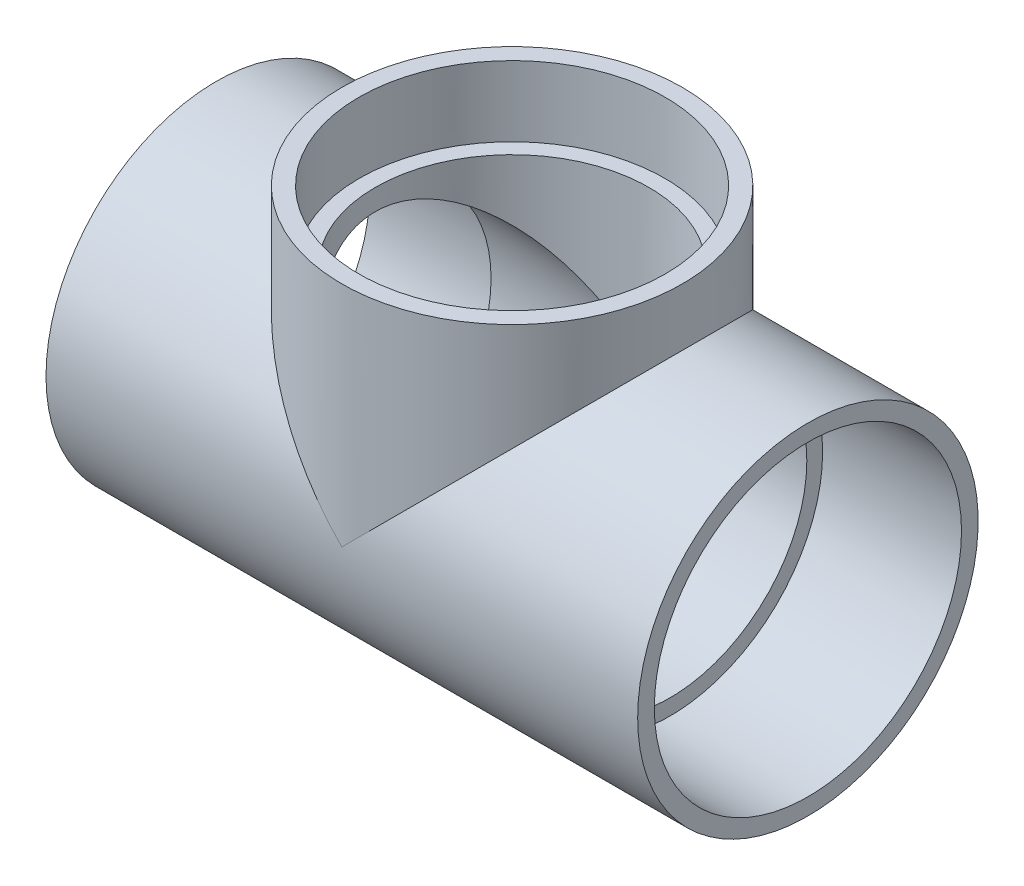
SolidWorks part; units mm, degrees
material "PVC Rigid"
ref_plane "Front Plane" through (0, 0, 0) normal (0, 0, 1) x (1, 0, 0)
ref_plane "Top Plane" through (0, 0, 0) normal (0, 1, 0) x (1, 0, 0)
ref_plane "Right Plane" through (0, 0, 0) normal (1, 0, 0) x (0, 0, -1)
sketch "Sketch0" plane through (0, 0, 0) normal (0, 0, 1) x (1, 0, 0)
  line L0 (-110.5154, 0) -> (0, 0) construction
  line L1 (0, 0) -> (0, 110.5154) construction
  line L2 (-58.9788, 0) -> (0, 0) construction
  line L3 (0, 0) -> (0, 58.9788) construction
  line L4 (-110.5154, 63.6016) -> (-110.5154, -63.6016) construction
  line L5 (-58.9788, 57.0357) -> (-110.5154, 57.3786) construction
  line L6 (-58.9788, 57.0357) -> (-58.9788, -57.0357) construction
  line L7 (-58.9788, -57.0357) -> (-110.5154, -57.3786) construction
  line L8 (-110.5154, 57.3786) -> (-110.5154, -57.3786) construction
  line L9 (-63.6016, 110.5154) -> (63.6016, 110.5154) construction
  line L10 (-57.3786, 110.5154) -> (57.3786, 110.5154) construction
  line L11 (57.3786, 110.5154) -> (57.0357, 58.9788) construction
  line L12 (57.0357, 58.9788) -> (-57.0357, 58.9788) construction
  line L13 (-57.0357, 58.9788) -> (-57.3786, 110.5154) construction
  line L14 (-58.9788, 51.1302) -> (-58.9788, -51.1302) construction
  line L15 (-110.5154, 0) -> (-58.9788, 0) construction
  line L16 (0, 110.5154) -> (0, 58.9788) construction
  line L17 (0, 0) -> (58.9788, 0) construction
  line L18 (-51.1302, 58.9788) -> (51.1302, 58.9788) construction
  line L19 (58.9788, 0) -> (110.5154, 0) construction
  dimension "H" = 110.5154
  dimension "G" = 58.9788
  dimension "M" = 127.2032
  dimension "OD A" = 114.7572
  dimension "OD B" = 114.0714
  dimension "ID" = 102.2604
  dimension "H3" = 110.5154
sketch "Sketch1" plane through (0, 0, 0) normal (0, 0, 1) x (1, 0, 0)
  line L0 (-110.5154, 0) -> (0, 0) construction
  line L1 (-110.5154, 0) -> (0, 0) construction
  line L2 (0, 0) -> (0, -63.6016) construction
  line L3 (-110.5154, -63.6016) -> (-58.9788, -63.6016)
  line L4 (-110.5154, -63.6016) -> (-110.5154, -57.3786)
  line L5 (-110.5154, -57.3786) -> (-58.9788, -57.0357)
  line L6 (-58.9788, -63.6016) -> (-58.9788, -57.0357)
  line L7 (-58.9788, -63.6016) -> (0, -63.6016) construction
  line L8 (110.5154, -57.3786) -> (58.9788, -57.0357)
  line L9 (110.5154, -63.6016) -> (110.5154, -57.3786)
  line L10 (58.9788, -63.6016) -> (58.9788, -57.0357)
  line L11 (110.5154, -63.6016) -> (58.9788, -63.6016)
revolve "Revolve1" add sketch "Sketch1" angle 360 about L1
sketch "Sketch2" plane through (0, 0, 0) normal (0, 0, 1) x (1, 0, 0)
  line L0 (57.3786, 110.5154) -> (57.0357, 58.9788)
  line L1 (57.0357, 58.9788) -> (63.6016, 58.9788)
  line L2 (63.6016, 58.9788) -> (63.6016, 110.5154)
  line L3 (63.6016, 110.5154) -> (57.3786, 110.5154)
  line L4 (0, 0) -> (0, 110.5154) construction
  line L5 (0, 0) -> (0, 110.5154) construction
revolve "Revolve2" add sketch "Sketch2" angle 360 about L5
sketch "Sketch3" plane through (-58.9788, 0, 0) normal (1, 0, 0) x (0, 0, -1)
  circle A0 centre (0, 0) radius 51.1302
  circle A1 centre (0, 0) radius 63.6016
sketch "Sketch4" plane through (-58.9788, 0, 0) normal (1, 0, 0) x (0, 0, -1)
  circle A0 centre (0, 0) radius 63.6016 construction
  circle A1 centre (0, 0) radius 63.6016
extrude "Boss-Extrude1" add sketch "Sketch4" along normal up to vertex
sketch "Sketch5" plane through (0, 58.9788, 0) normal (0, -1, 0) x (1, 0, 0)
  circle A0 centre (0, 0) radius 63.6016 construction
  circle A1 centre (0, 0) radius 63.6016
extrude "Boss-Extrude2" add sketch "Sketch5" along normal up to vertex (58.9788 mm away) up to point (0, 0, 0)
sketch "Sketch6" plane through (0, 0, 0) normal (0, 0, 1) x (1, 0, 0)
  line L0 (-110.5154, -57.3786) -> (-58.9788, -57.0357)
  line L1 (-58.9788, -57.0357) -> (-58.9788, -51.1302)
  line L2 (-58.9788, -51.1302) -> (58.9788, -51.1302)
  line L3 (58.9788, -57.0357) -> (58.9788, 51.8306) construction
  line L4 (0, -51.1302) -> (0, 0) construction
  line L5 (58.9788, -57.0357) -> (58.9788, -51.1302)
  line L6 (110.5154, -57.3786) -> (110.5154, 57.3786) construction
  line L7 (110.5154, -63.6016) -> (110.5154, 63.6016) construction
  line L8 (110.5154, -57.3786) -> (110.5154, 0)
  line L9 (110.5154, 0) -> (-110.5154, 0)
  line L10 (-110.5154, 0) -> (-110.5154, -57.3786)
  line L11 (110.5154, -57.3786) -> (58.9788, -57.0357)
revolve "Cut-Revolve1" cut sketch "Sketch6" angle 360 about L9
sketch "Sketch7" plane through (0, 0, 0) normal (0, 0, 1) x (1, 0, 0)
  line L0 (57.3786, 110.5154) -> (57.0357, 58.9788)
  line L1 (57.0357, 58.9788) -> (51.1302, 58.9788)
  line L2 (51.1302, 58.9788) -> (51.1302, 0)
  line L3 (0, 0) -> (58.9788, 0) construction
  line L4 (51.1302, 0) -> (0, 0)
  line L5 (0, 0) -> (0, 110.5154)
  line L6 (-63.6016, 110.5154) -> (63.6016, 110.5154) construction
  line L7 (0, 110.5154) -> (57.3786, 110.5154)
revolve "Cut-Revolve2" cut sketch "Sketch7" angle 360 about L5
sketch "Sketch8" plane through (0, 110.5154, 0) normal (0, 1, 0) x (1, 0, 0)
  circle A0 centre (0, 0) radius 92.1901
  circle A1 centre (0, 0) radius 25.0502
extrude "Cut-Extrude1" cut sketch "Sketch8" against normal blind 25.4
